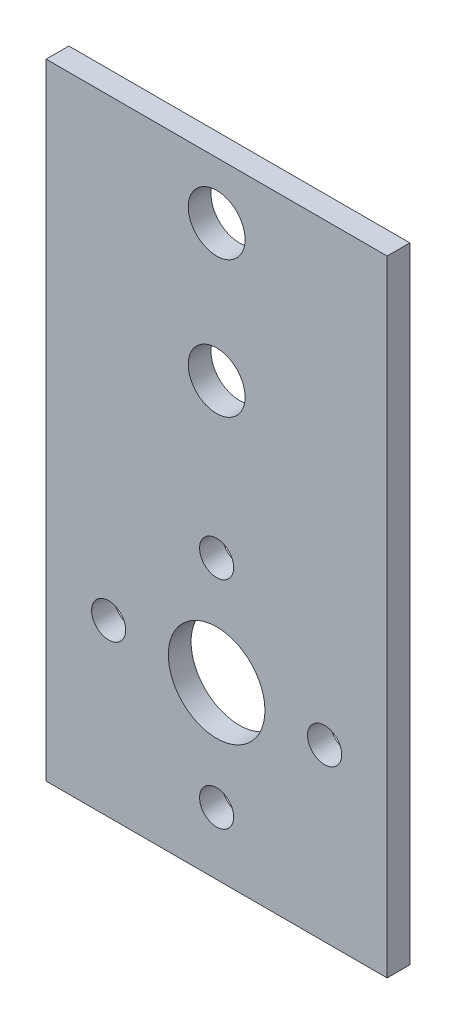
SolidWorks part; units mm, degrees
ref_plane "Front Plane" through (0, 0, 0) normal (0, 0, 1) x (1, 0, 0)
ref_plane "Top Plane" through (0, 0, 0) normal (0, 1, 0) x (1, 0, 0)
ref_plane "Right Plane" through (0, 0, 0) normal (1, 0, 0) x (0, 0, -1)
sketch "Sketch1" plane through (0, 0, 0) normal (0, 0, 1) x (1, 0, 0)
  line L1 (-15, 15) -> (15, 15)
  line L2 (-15, 15) -> (-15, -15)
  line L3 (-15, -15) -> (15, -15)
  line L4 (15, 15) -> (15, -15)
  line L5 (-15, 15) -> (15, -15) construction
  line L6 (-15, -15) -> (15, 15) construction
  circle A0 centre (0, 0) radius 4.25
  circle A1 centre (0, 9.5) radius 1.5
  circle A2 centre (9.5, 0) radius 1.5
  circle A3 centre (0, -9.5) radius 1.5
  circle A4 centre (-9.5, 0) radius 1.5
  point P0 (0, 0)
  dimension "D3" = 4
  dimension "D4" = 8.5
  dimension "D5" = 3
  dimension "D6" = 3
  dimension "D1" = 30
  dimension "D2" = 30
  dimension "D7" = 9.5
extrude "Boss-Extrude1" add sketch "Sketch1" along normal blind 2
sketch "Sketch2" plane through (0, 15, 0) normal (0, 1, 0) x (1, 0, 0)
  line L1 (-15, -2) -> (15, -2)
  line L2 (-15, -2) -> (-15, 0)
  line L3 (-15, 0) -> (15, 0)
  line L4 (15, -2) -> (15, 0)
  line L5 (-15, -2) -> (15, 0) construction
  line L6 (-15, 0) -> (15, -2) construction
  point P0 (0, -1)
  dimension "D1" = 30
  dimension "D2" = 2
extrude "Boss-Extrude2" add sketch "Sketch2" along normal blind 25
sketch "Sketch3" plane through (0, 0, 2) normal (0, 0, 1) x (1, 0, 0)
  line L0 (-15, 40) -> (15, 40) construction
  circle A0 centre (0, 23) radius 2.5
  circle A1 centre (0, 35) radius 2.5
  dimension "D1" = 5
  dimension "D2" = 12
extrude "Cut-Extrude1" cut sketch "Sketch3" against normal blind 2
